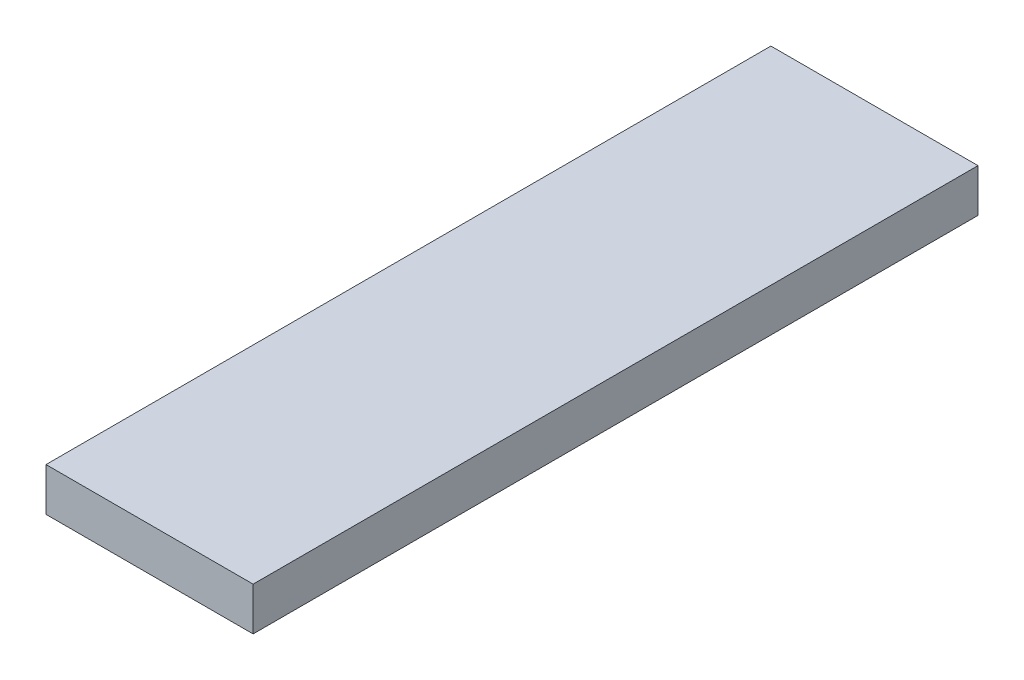
SolidWorks part; units mm, degrees
ref_plane "Front" through (0, 0, 0) normal (0, 0, 1) x (1, 0, 0)
ref_plane "Top" through (0, 0, 0) normal (0, 1, 0) x (1, 0, 0)
ref_plane "Right" through (0, 0, 0) normal (1, 0, 0) x (0, 0, -1)
sketch "Sketch1" plane through (0, 0, 0) normal (0, 0, 1) x (1, 0, 0)
  line L1 (0, 0) -> (-15.24, 0)
  line L2 (0, 0) -> (0, 3.175)
  line L3 (0, 3.175) -> (-15.24, 3.175)
  line L4 (-15.24, 0) -> (-15.24, 3.175)
  dimension "D1" = 15.24
  dimension "D2" = 3.175
extrude "Boss-Extrude1" add sketch "Sketch1" along normal blind 53.34
